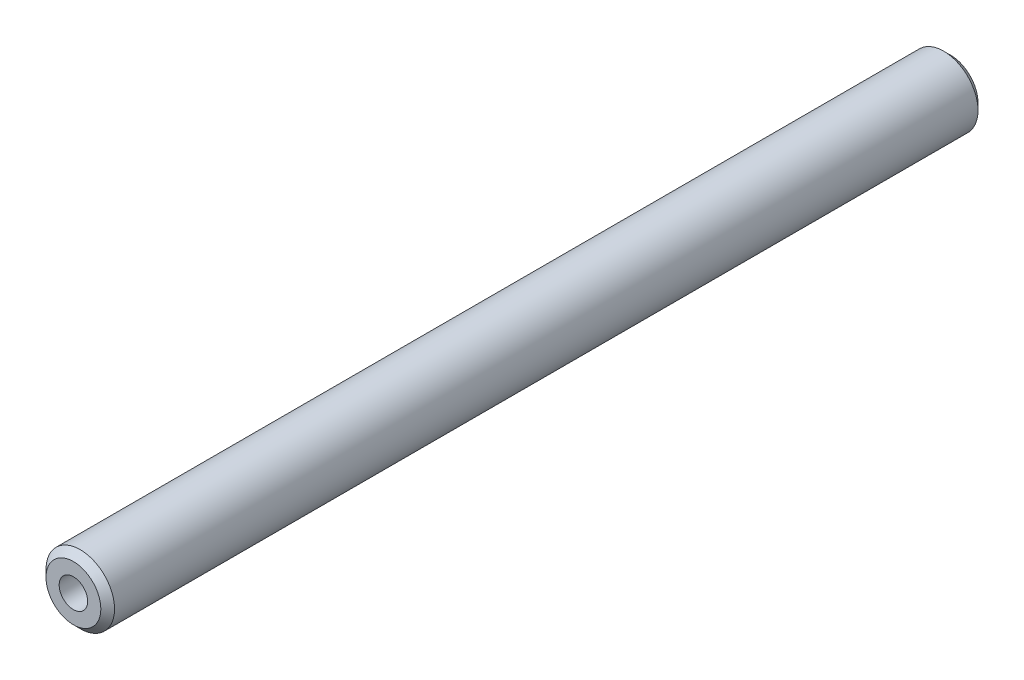
SolidWorks part; units mm, degrees
ref_plane "Front" through (0, 0, 0) normal (0, 0, 1) x (1, 0, 0)
ref_plane "Top" through (0, 0, 0) normal (0, 1, 0) x (1, 0, 0)
ref_plane "Right" through (0, 0, 0) normal (1, 0, 0) x (0, 0, -1)
sketch "Sketch1" plane through (0, 0, 0) normal (0, 0, 1) x (1, 0, 0)
  circle A0 centre (0, 0) radius 3.9688
  dimension "dia" = 7.9375
sketch "Sketch2" plane through (0, 0, 0) normal (1, 0, 0) x (0, 0, -1)
  line L0 (-50.8, 0) -> (50.8, 0) construction
  line L1 (5.2388, 0) -> (-5.2388, 0) construction
  line L3 (50.8, 3.9687) -> (50.8, -3.9688) construction
  line L4 (-50.8, 3.9688) -> (-50.8, -3.9687) construction
  line L5 (-31.75, 3.9688) -> (-31.75, -3.9688) construction
  line L6 (31.75, 3.9688) -> (31.75, -3.9688) construction
  point P6 (0, 0)
  point P10 (50.8, 0)
  point P13 (-50.8, 0)
  point P16 (-31.75, 0)
  point P19 (31.75, 0)
  dimension "D1" = 7.9375
  dimension "lg" = 101.6
  dimension "D2" = 19.05
  dimension "D3" = 19.05
sketch "Sketch3" plane through (0, 0, 0) normal (0, 0, 1) x (1, 0, 0)
  line L0 (0, 3.9688) -> (0, -3.9687) construction
  circle A0 centre (0, 0) radius 3.9688
  dimension "D1" = 7.9375
extrude "Boss-Extrude1" add sketch "Sketch3" along normal mid plane 101.6
chamfer "Chamfer1" distance 0.7937 angle 45 2 edges at (3.9688, 0, -50.8) (3.9688, 0, 50.8)
sketch "Sketch4" plane through (0, 0, -50.8) normal (0, 0, -1) x (-1, 0, 0)
  point P0 (0, 0)
hole_wizard "M4x0.7 Tapped Hole1" positions "Sketch5" profile "Sketch6" tap size "M4x0.7" standard "ANSI Metric"
sketch "Sketch5" plane through (0, 0, -50.8) normal (0, 0, -1) x (-1, 0, 0)
  point P0 (0, 0)
cosmetic thread "Hole Thread1" parameters "D1"=15, "D2"=4
sketch "Sketch6" plane through (0, 0, -50.8) normal (1, 0, 0) x (0, 1, 0)
  line L0 (0, 0) -> (0, 15.9914)
  line L1 (0, 15.9914) -> (1.65, 15)
  line L2 (1.65, 15) -> (1.65, 0)
  line L5 (1.65, 0) -> (0, 0)
  line L10 (0, 15.9914) -> (-1.65, 15) construction
  line L11 (0, -6.35) -> (0, 107.95) construction
  dimension "Tap Drill Dia." = 3.3
  dimension "Tap Drill Depth" = 15
  dimension "Drill Angle" = 118
mirror "Mirror1" about plane through (0, 0, 0) normal (0, 0, 1) of "M4x0.7 Tapped Hole1"
equation "\"D1@Sketch2\"=\"dia@sketch1\""
equation "\"D1@Sketch3\"=\"dia@Sketch1\""
equation "\"D1@Boss-Extrude1\"=\"lg@Sketch2\""
equation "\"D1@Chamfer1\"=\"dia@Sketch1\"*.1"
